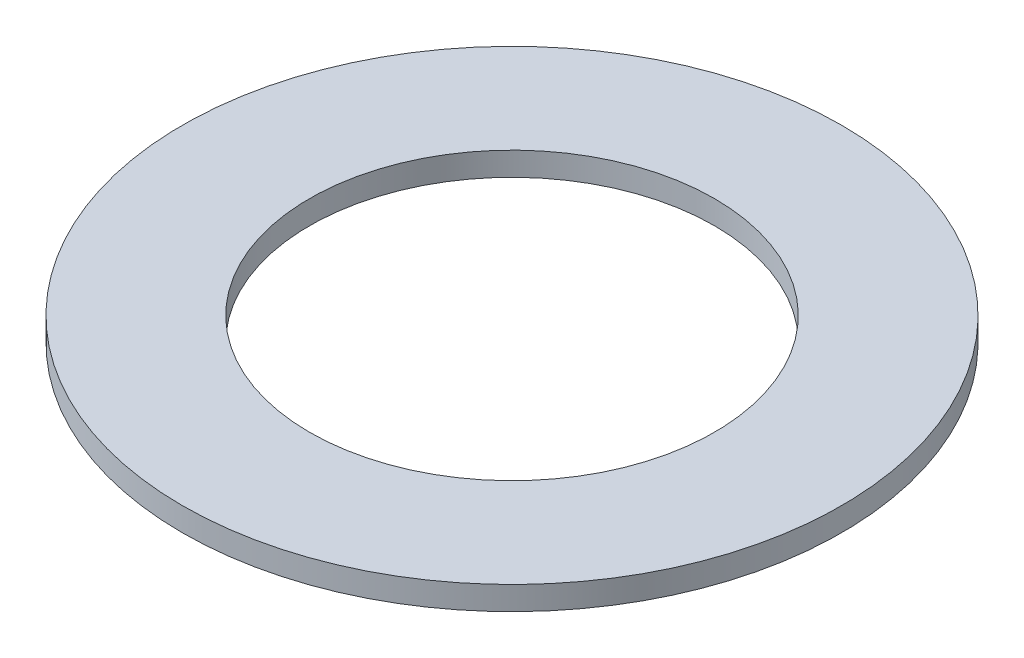
SolidWorks part; units mm, degrees
ref_plane "Front Plane" through (0, 0, 0) normal (0, 0, 1) x (1, 0, 0)
ref_plane "Top Plane" through (0, 0, 0) normal (0, 1, 0) x (1, 0, 0)
ref_plane "Right Plane" through (0, 0, 0) normal (1, 0, 0) x (0, 0, -1)
sketch "Sketch1" plane through (0, 0, 0) normal (0, 1, 0) x (1, 0, 0)
  circle A0 centre (0, 0) radius 7
  circle A1 centre (0, 0) radius 4.3
  dimension "D1" = 8.6
  dimension "D2" = 14
extrude "Boss-Extrude1" add sketch "Sketch1" along normal blind 0.5
